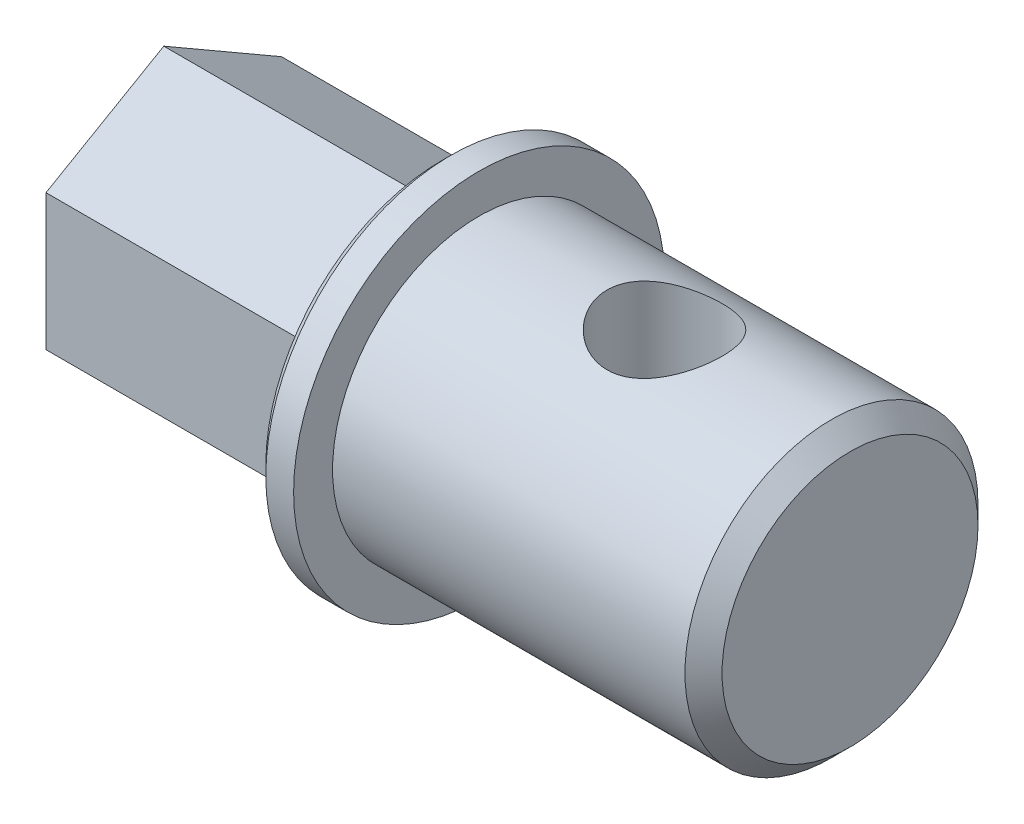
SolidWorks part; units mm, degrees
ref_plane "前视基准面" through (0, 0, 0) normal (0, 0, 1) x (1, 0, 0)
ref_plane "上视基准面" through (0, 0, 0) normal (0, 1, 0) x (1, 0, 0)
ref_plane "右视基准面" through (0, 0, 0) normal (1, 0, 0) x (0, 0, -1)
sketch "草图1" plane through (0, 0, 0) normal (1, 0, 0) x (0, 0, -1)
  circle A0 centre (0, 0) radius 7.9
extrude "凸台-拉伸1" add sketch "草图1" along normal blind 20
sketch "草图3" plane through (0, 0, 0) normal (-1, 0, 0) x (0, 0, 1)
  circle A0 centre (0, 0) radius 10
extrude "凸台-拉伸2" add sketch "草图3" along normal blind 2
sketch "草图4" plane through (-2, 0, 0) normal (-1, 0, 0) x (0, 0, 1)
  line L0 (0, 0) -> (0, 5) construction
  line L1 (6.35, 3.6662) -> (0, 7.3323)
  line L2 (0, 7.3323) -> (-6.35, 3.6662)
  line L3 (-6.35, 3.6662) -> (-6.35, -3.6662)
  line L4 (-6.35, -3.6662) -> (0, -7.3323)
  line L5 (0, -7.3323) -> (6.35, -3.6662)
  line L6 (6.35, -3.6662) -> (6.35, 3.6662)
  circle A0 centre (0, 0) radius 6.35 construction
  dimension "D1" = 12.7
  dimension "D2" = 60
extrude "凸台-拉伸3" add sketch "草图4" along normal blind 15
sketch "草图5" plane through (0, 0, 0) normal (0, 1, 0) x (1, 0, 0)
  line L0 (20, 0) -> (10, 0) construction
  line L1 (20, -7.9) -> (20, 7.9) construction
  circle A0 centre (10, 0) radius 3.1
  dimension "D1" = 6.2
chamfer "倒角1" distance 0.5 angle 45 1 edges at (-2, 0, 10)
hole_wizard "M5x0.8 螺纹孔1" positions "草图6" profile "草图7" tap size "M5x0.8" standard "ANSI Metric"
sketch "草图6" plane through (-17, 0, 0) normal (-1, 0, 0) x (0, 0, 1)
  point P0 (0, 0)
sketch "草图7" plane through (-17, 0, 0) normal (0, 1, 0) x (0, 0, 1)
  line L0 (0, 0) -> (0, 13.6618)
  line L1 (0, 13.6618) -> (2.1, 12.4)
  line L2 (2.1, 12.4) -> (2.1, 0)
  line L5 (2.1, 0) -> (0, 0)
  line L10 (0, 13.6618) -> (-2.1, 12.4) construction
  line L11 (0, -6.35) -> (0, 107.95) construction
  dimension "螺纹孔钻头直径" = 4.2
  dimension "螺纹孔钻头深度" = 12.4
  dimension "导头角度" = 118
cosmetic thread "孔螺蚊线1" parameters "D1"=10, "D2"=5
sketch3d "3D草图1"
  circle A0 centre (10, 7.9, 0) radius 3.1
  point P2 (10, 11, 0)
  dimension "D1" = 7.9
extrude "切除-拉伸1" cut sketch "草图5" against normal through all both and the other way through all
chamfer "倒角2" distance 1 angle 45 1 edges at (20, 0, -7.9)
